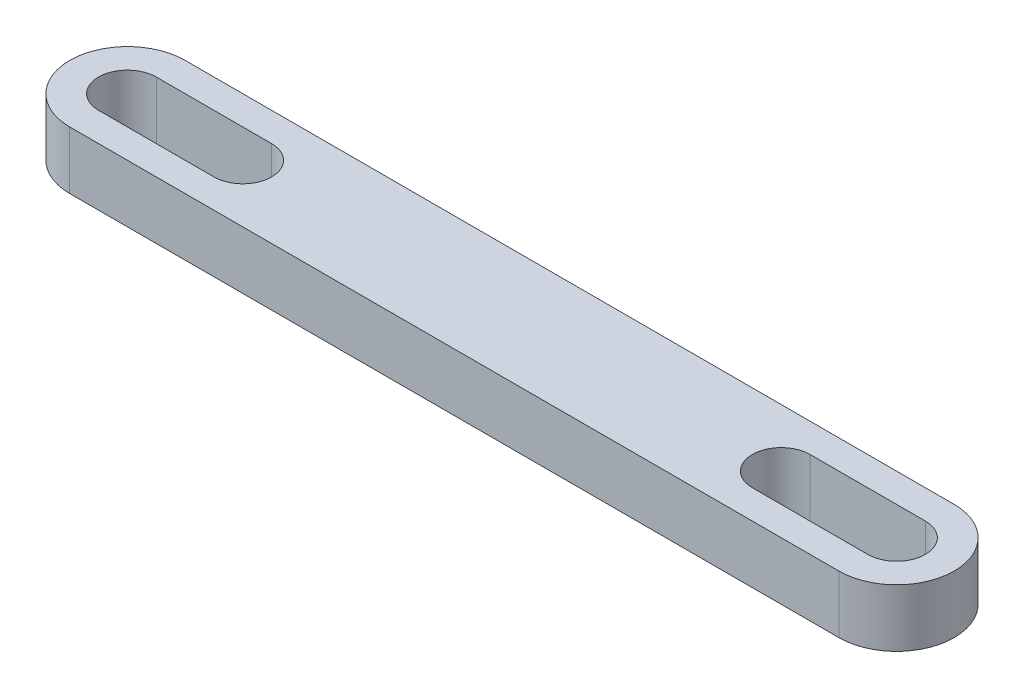
SolidWorks part; units mm, degrees
ref_plane "Front Plane" through (0, 0, 0) normal (0, 0, 1) x (1, 0, 0)
ref_plane "Top Plane" through (0, 0, 0) normal (0, 1, 0) x (1, 0, 0)
ref_plane "Right Plane" through (0, 0, 0) normal (1, 0, 0) x (0, 0, -1)
sketch "Sketch1" plane through (0, 0, 0) normal (0, 1, 0) x (1, 0, 0)
  line L0 (-20, 6) -> (-20, 0) construction
  line L1 (0, 0) -> (-40, 0)
  line L3 (0, 6) -> (-40, 6)
  line L5 (-40, 4.5) -> (-34, 4.5)
  line L7 (-40, 1.5) -> (-34, 1.5)
  line L10 (0, 1.5) -> (-6, 1.5)
  line L12 (0, 4.5) -> (-6, 4.5)
  arc A0 (-40, 6) -> (-40, 0) centre (-40, 3) ccw
  arc A1 (0, 6) -> (0, 0) centre (0, 3) cw
  arc A2 (-40, 4.5) -> (-40, 1.5) centre (-40, 3) ccw
  arc A3 (0, 4.5) -> (0, 1.5) centre (0, 3) cw
  arc A4 (-34, 1.5) -> (-34, 4.5) centre (-34, 3) ccw
  arc A5 (-6, 4.5) -> (-6, 1.5) centre (-6, 3) ccw
  dimension "D3" = 6
  dimension "D4" = 3
  dimension "D7" = 3
  dimension "D1" = 40
  dimension "D2" = 6
  dimension "D5" = 6
  dimension "D6" = 6
extrude "Boss-Extrude1" add sketch "Sketch1" along normal blind 3 contours A2 | A3 | L3 A0 L1 A1
